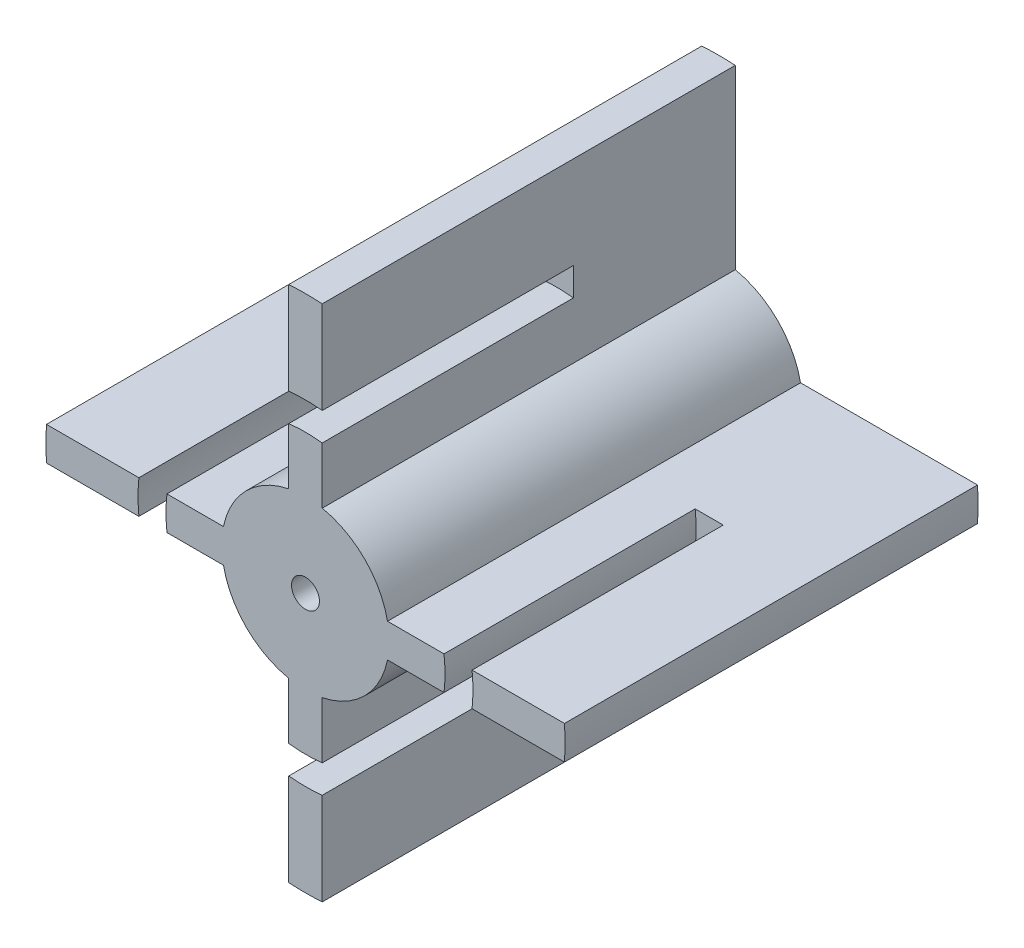
SolidWorks part; units mm, degrees
ref_plane "Front Plane" through (0, 0, 0) normal (0, 0, 1) x (1, 0, 0)
ref_plane "Top Plane" through (0, 0, 0) normal (0, 1, 0) x (1, 0, 0)
ref_plane "Right Plane" through (0, 0, 0) normal (1, 0, 0) x (0, 0, -1)
sketch "Sketch1" plane through (0, 0, 0) normal (0, 0, 1) x (1, 0, 0)
  circle A0 centre (0, 0) radius 46.5
  dimension "D1" = 93
extrude "Boss-Extrude1" add sketch "Sketch1" along normal blind 74
sketch "Sketch2" plane through (0, 0, 74) normal (0, 0, 1) x (1, 0, 0)
  circle A0 centre (0, 0) radius 2.5
  dimension "D1" = 5
extrude "Cut-Extrude1" cut sketch "Sketch2" against normal blind 10
sketch "Sketch3" plane through (0, 0, 0) normal (0, 0, -1) x (-1, 0, 0)
  circle A0 centre (0, 0) radius 2.5
  dimension "D1" = 5
extrude "Cut-Extrude2" cut sketch "Sketch3" against normal blind 10
sketch "Sketch4" plane through (0, 0, 0) normal (0, 0, -1) x (-1, 0, 0)
  line L0 (0, -46.5) -> (0, -15) construction
  line L1 (15, 0) -> (46.5, 0) construction
  line L2 (0, 7.8049) -> (0, 46.5) construction
  line L3 (-15, 0) -> (-46.5, 0) construction
  line L4 (-46.4031, 3) -> (-14.6969, 3)
  line L6 (-14.6969, -3) -> (-46.4031, -3)
  line L7 (-3, -14.6969) -> (-3, -46.4031)
  line L9 (3, -46.4031) -> (3, -14.6969)
  line L10 (14.6969, 3) -> (46.4031, 3)
  line L12 (46.4031, -3) -> (14.6969, -3)
  line L13 (3, 46.4031) -> (3, 14.6969)
  line L15 (-3, 14.6969) -> (-3, 46.4031)
  arc A0 (-3, 14.6969) -> (-14.6969, 3) centre (0, 0) ccw
  arc A1 (46.4031, -3) -> (46.4031, 3) centre (0, 0) ccw
  circle A2 centre (0, 0) radius 46.5 construction
  arc A3 (-14.6969, -3) -> (-3, -14.6969) centre (0, 0) ccw
  arc A4 (14.6969, 3) -> (3, 14.6969) centre (0, 0) ccw
  arc A5 (3, -14.6969) -> (14.6969, -3) centre (0, 0) ccw
  arc A6 (-3, -46.4031) -> (3, -46.4031) centre (0, 0) ccw
  arc A7 (-46.4031, 3) -> (-46.4031, -3) centre (0, 0) ccw
  arc A8 (3, 46.4031) -> (-3, 46.4031) centre (0, 0) ccw
  dimension "D8" = 15
  dimension "D1" = 3
  dimension "D2" = 3
  dimension "D3" = 3
  dimension "D4" = 3
  dimension "D5" = 3
  dimension "D6" = 3
  dimension "D7" = 3
extrude "Cut-Extrude3" cut sketch "Sketch4" against normal through all flip side to cut
sketch "Sketch5" plane through (0, 0, 0) normal (0, 0, 1) x (1, 0, 0)
  circle A0 centre (-9.3234, 9.512) radius 2.5
  circle A1 centre (9.5329, -9.2187) radius 2.5
  dimension "D1" = 5
  dimension "D2" = 5
extrude "Boss-Extrude2" [suppressed] add sketch "Sketch5" along normal blind 15 separate body
sketch "Sketch7" plane through (0, 0, 74) normal (0, 0, 1) x (1, 0, 0)
  circle A0 centre (0, 0) radius 25
  circle A1 centre (0, 0) radius 30
  dimension "D1" = 50
  dimension "D2" = 60
extrude "Cut-Extrude4" cut sketch "Sketch7" against normal blind 45
